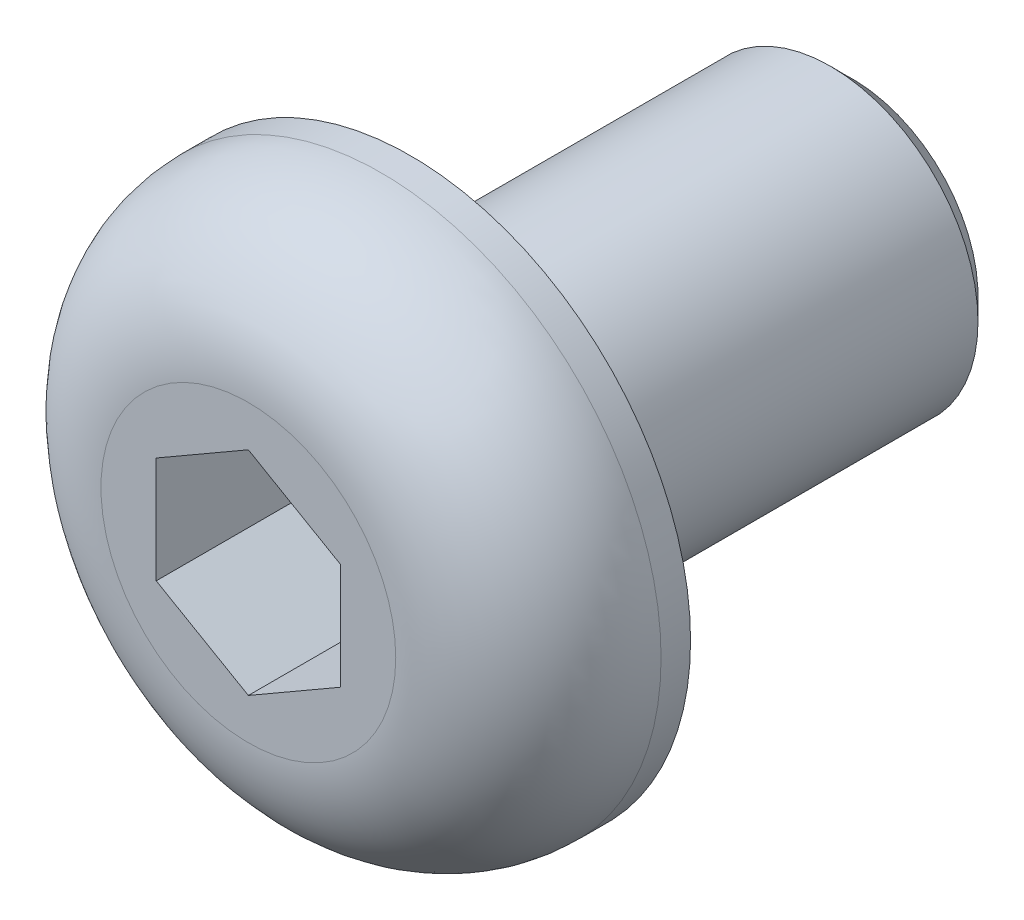
SolidWorks part; units mm, degrees
ref_plane "Front Plane" through (0, 0, 0) normal (0, 0, 1) x (1, 0, 0)
ref_plane "Top Plane" through (0, 0, 0) normal (0, 1, 0) x (1, 0, 0)
ref_plane "Right Plane" through (0, 0, 0) normal (1, 0, 0) x (0, 0, -1)
sketch "Sketch1" plane through (0, 0, 0) normal (0, 0, 1) x (1, 0, 0)
  circle A0 centre (0, 0) radius 3.8
  dimension "D1" = 7.6
extrude "Boss-Extrude1" add sketch "Sketch1" along normal blind 2.2
sketch "Sketch2" plane through (0, 0, 0) normal (0, 0, -1) x (-1, 0, 0)
  circle A0 centre (0, 0) radius 2
  dimension "D1" = 4
extrude "Boss-Extrude2" add sketch "Sketch2" along normal blind 6
chamfer "Chamfer1" distance 0.3 angle 45 1 edges at (-2, 0, -6)
sketch "Sketch3" plane through (0, 0, 2.2) normal (0, 0, 1) x (1, 0, 0)
  line L1 (0, 1.4434) -> (-1.25, 0.7217)
  line L2 (-1.25, 0.7217) -> (-1.25, -0.7217)
  line L3 (-1.25, -0.7217) -> (0, -1.4434)
  line L4 (0, -1.4434) -> (1.25, -0.7217)
  line L5 (1.25, -0.7217) -> (1.25, 0.7217)
  line L6 (1.25, 0.7217) -> (0, 1.4434)
  circle A0 centre (0, 0) radius 1.25 construction
  dimension "D1" = 2.5
extrude "Cut-Extrude1" cut sketch "Sketch3" against normal blind 2
fillet "Fillet1" radius 1.8 1 edges at (3.8, 0, 2.2)
